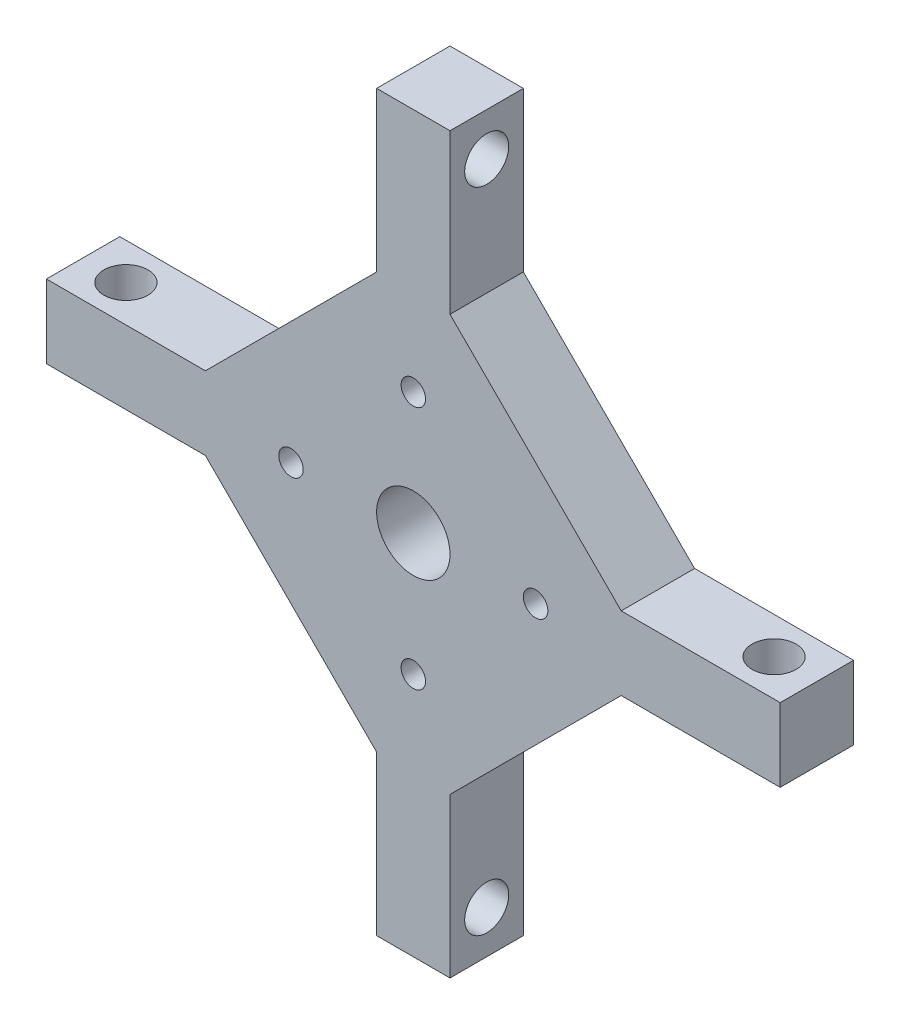
SolidWorks part; units mm, degrees
ref_plane "Front Plane" through (0, 0, 0) normal (0, 0, 1) x (1, 0, 0)
ref_plane "Top Plane" through (0, 0, 0) normal (0, 1, 0) x (1, 0, 0)
ref_plane "Right Plane" through (0, 0, 0) normal (1, 0, 0) x (0, 0, -1)
sketch "Sketch1" plane through (0, 0, 0) normal (0, 0, 1) x (1, 0, 0)
  line L0 (0, 0) -> (30, 0) construction
  line L1 (30, 0) -> (30, 3) construction
  line L2 (3, -30) -> (-3, -30)
  line L3 (30, 3) -> (17, 3)
  line L4 (30, 3) -> (30, -3)
  line L5 (30, -3) -> (17, -3)
  line L6 (17, 3) -> (17, -3)
  line L7 (3, -30) -> (3, -17)
  line L8 (3, -17) -> (-3, -17)
  line L9 (-3, -30) -> (-3, -17)
  line L10 (-30, -3) -> (-30, 3)
  line L11 (-30, -3) -> (-17, -3)
  line L12 (-17, -3) -> (-17, 3)
  line L13 (-30, 3) -> (-17, 3)
  line L14 (-3, 30) -> (3, 30)
  line L15 (-3, 30) -> (-3, 17)
  line L16 (-3, 17) -> (3, 17)
  line L17 (3, 30) -> (3, 17)
  line L18 (-3, 17) -> (-17, 3)
  line L19 (-17, -3) -> (-3, -17)
  line L20 (3, -17) -> (17, -3)
  line L21 (17, 3) -> (3, 17)
  point P22 (0, 0)
  dimension "D1" = 30
  dimension "D2" = 6
  dimension "D3" = 3
  dimension "D4" = 13
  dimension "D5" = 4
extrude "Boss-Extrude1" add sketch "Sketch1" along normal blind 6
sketch "Sketch2" plane through (3, 0, 0) normal (1, 0, 0) x (0, 0, -1)
  line L0 (-6, 30) -> (0, 30) construction
  circle A0 centre (-3, 26.5) radius 1.8
  dimension "D1" = 3.6
  dimension "D2" = 3.5
extrude "Cut-Extrude1" cut sketch "Sketch2" against normal blind 6
pattern_circular "CirPattern1" count 4 over 360 about axis through (0, 0, 6) along (0, 0, 1) of "Cut-Extrude1"
sketch "Sketch3" plane through (0, 0, 6) normal (0, 0, 1) x (1, 0, 0)
  circle A0 centre (0, 0) radius 3
  dimension "D1" = 6
extrude "Cut-Extrude2" cut sketch "Sketch3" against normal through all contours A0
sketch "Sketch4" plane through (0, 0, 6) normal (0, 0, 1) x (1, 0, 0)
  circle A0 centre (0, 10) radius 1
  dimension "D1" = 10
extrude "Cut-Extrude3" cut sketch "Sketch4" against normal blind 10
pattern_circular "CirPattern2" count 4 over 360 about axis through (0, 0, 0) along (0, 0, 1) of "Cut-Extrude3"
